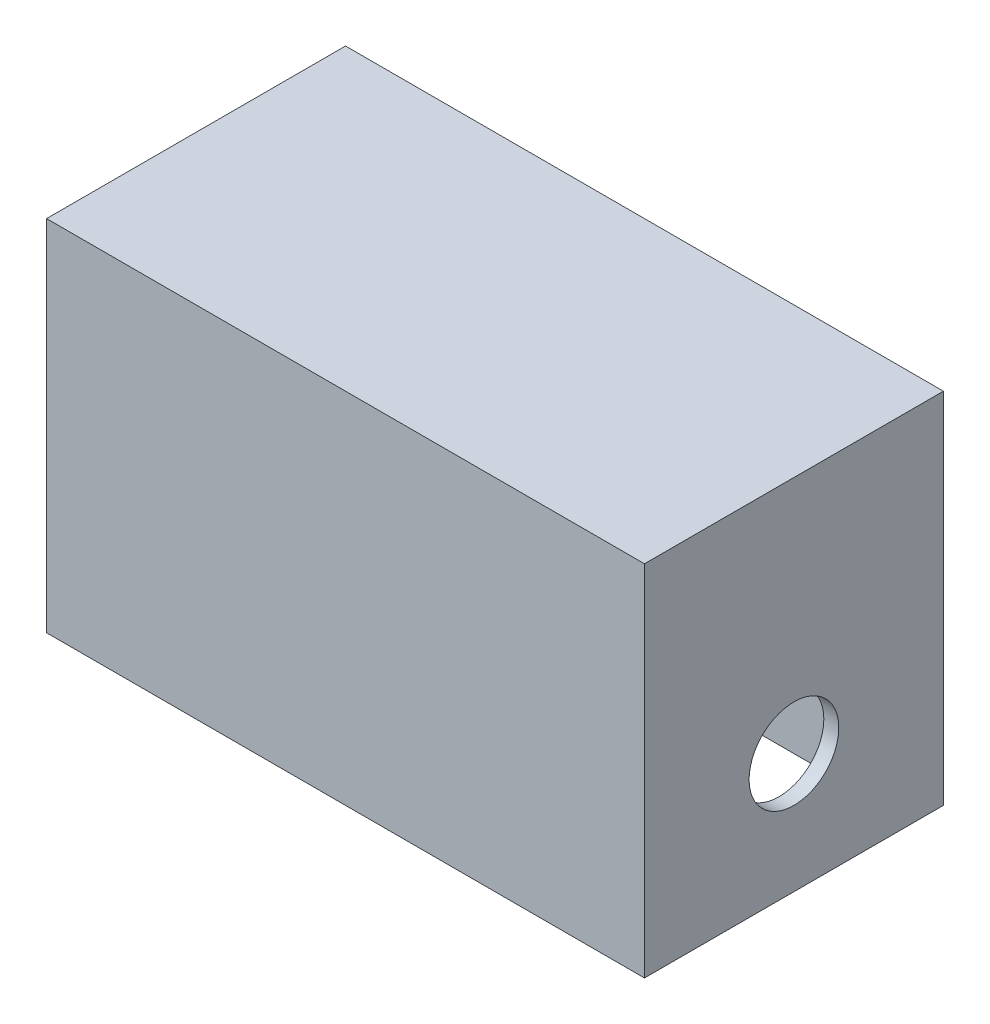
SolidWorks part; units mm, degrees
ref_plane "Front Plane" through (0, 0, 0) normal (0, 0, 1) x (1, 0, 0)
ref_plane "Top Plane" through (0, 0, 0) normal (0, 1, 0) x (1, 0, 0)
ref_plane "Right Plane" through (0, 0, 0) normal (1, 0, 0) x (0, 0, -1)
sketch "Sketch1" plane through (0, 0, 0) normal (0, 0, 1) x (1, 0, 0)
  line L1 (0, 0) -> (100, 0)
  line L2 (0, 0) -> (0, 60)
  line L3 (0, 60) -> (100, 60)
  line L4 (100, 0) -> (100, 60)
  dimension "D1" = 100
  dimension "D2" = 60
extrude "Boss-Extrude1" add sketch "Sketch1" along normal blind 50
sketch "Sketch2" plane through (0, 0, 0) normal (0, -1, 0) x (1, 0, 0)
  line L1 (2.5, 45) -> (97.5, 45)
  line L2 (2.5, 45) -> (2.5, 5)
  line L3 (2.5, 5) -> (97.5, 5)
  line L4 (97.5, 45) -> (97.5, 5)
  line L6 (100, 50) -> (100, 0) construction
  line L7 (0, 50) -> (100, 50) construction
  point P4 (50, 5)
  point P5 (2.5, 25)
  dimension "D1" = 50
  dimension "D2" = 25
  dimension "D3" = 40
  dimension "D4" = 95
extrude "Cut-Extrude1" cut sketch "Sketch2" against normal blind 55
sketch "Sketch3" plane through (0, 0, 0) normal (-1, 0, 0) x (0, 0, 1)
  line L0 (0, 60) -> (0, 0) construction
  circle A0 centre (25, 20) radius 7.5
  dimension "D1" = 15
  dimension "D3" = 25
  dimension "D2" = 20
extrude "Cut-Extrude2" cut sketch "Sketch3" against normal through all
